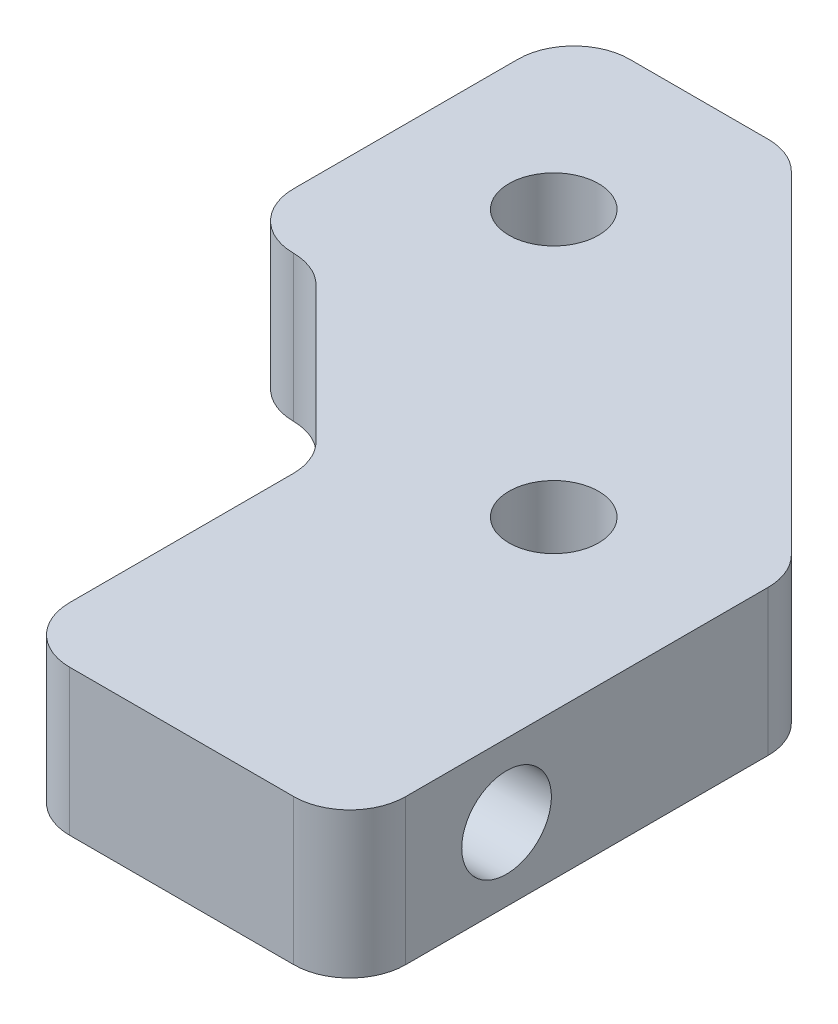
SolidWorks part; units mm, degrees
ref_plane "Front Plane" through (0, 0, 0) normal (0, 0, 1) x (1, 0, 0)
ref_plane "Top Plane" through (0, 0, 0) normal (0, 1, 0) x (1, 0, 0)
ref_plane "Right Plane" through (0, 0, 0) normal (1, 0, 0) x (0, 0, -1)
sketch "Sketch1" plane through (0, 0, 0) normal (0, 1, 0) x (1, 0, 0)
  line L1 (0, -15) -> (-15, 0)
  line L2 (0, -42) -> (30, -42)
  line L3 (-2.5736, 30) -> (30, -2.5736)
  line L4 (-22, 0) -> (-22, 30)
  line L5 (30, -2.5736) -> (30, -42)
  line L6 (-15, 0) -> (-22, 0)
  line L7 (0, -42) -> (0, -15)
  line L8 (-22, 30) -> (-2.5736, 30)
  circle A0 centre (-8.7868, 15) radius 4
  circle A1 centre (15, -8.7868) radius 4
extrude "Extrude1" add sketch "Sketch1" along normal blind 13
fillet "Fillet5" radius 5 6 edges at (0, 6.5, 42) (30, 6.5, 42) (30, 6.5, 2.5736) (-2.5736, 6.5, -30) (-15, 6.5, 0) (0, 6.5, 15)
fillet "Fillet6" radius 5 2 edges at (-22, 6.5, 0) (-22, 6.5, -30)
sketch "Sketch8" plane through (0, 0, 0) normal (-1, 0, 0) x (0, 0, 1)
  circle A0 centre (28, 6.5) radius 4
extrude "Extrude7" cut sketch "Sketch8" against normal blind 30
